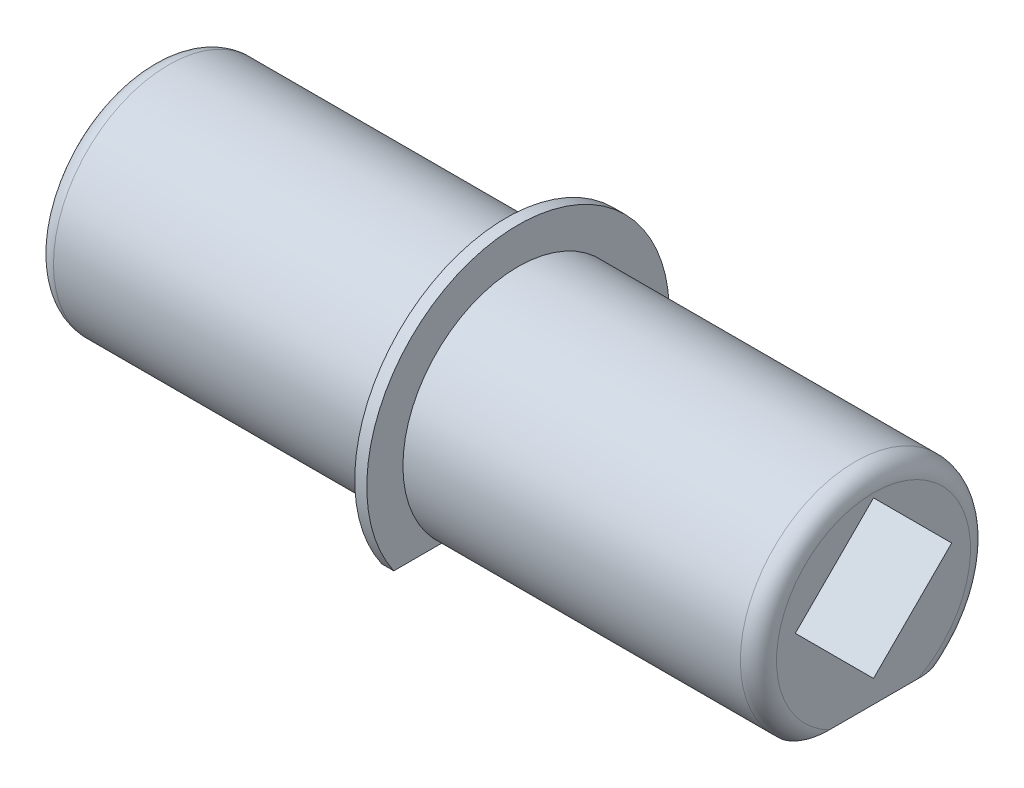
SolidWorks part; units mm, degrees
ref_plane "Plan de face" through (0, 0, 0) normal (0, 0, 1) x (1, 0, 0)
ref_plane "Plan de dessus" through (0, 0, 0) normal (0, 1, 0) x (1, 0, 0)
ref_plane "Plan de droite" through (0, 0, 0) normal (1, 0, 0) x (0, 0, -1)
sketch "Esquisse1" plane through (0, 0, 0) normal (1, 0, 0) x (0, 0, -1)
  line L0 (-6.3185, -7.161) -> (6.3185, -7.161)
  arc A0 (-6.3185, -7.161) -> (6.3185, -7.161) centre (0, 0) cw
  point P6 (0, -7.161)
  dimension "D1" = 9.55
extrude "Boss.-Extru.1" add sketch "Esquisse1" along normal mid plane 60
sketch "Esquisse3" plane through (0, 0, 0) normal (1, 0, 0) x (0, 0, -1)
  line L0 (-10.3065, -7.161) -> (10.3065, -7.161)
  line L1 (-6.3185, -7.161) -> (6.3185, -7.161) construction
  arc A2 (8.3034, -9.4105) -> (-8.3034, -9.4105) centre (0, 0) ccw
  arc A3 (10.3065, -7.161) -> (-10.3065, -7.161) centre (0, 0) ccw
  dimension "D1" = 3
extrude "Boss.-Extru.2" add sketch "Esquisse3" along normal mid plane 1
sketch "Esquisse2" plane through (0, 0, 0) normal (1, 0, 0) x (0, 0, -1)
  line L0 (0, 9.55) -> (0, 7.683) construction
  line L7 (0, -5.2939) -> (0, -7.161) construction
  line L8 (-6.3185, -7.161) -> (6.3185, -7.161) construction
  line L9 (-6.4884, 1.1945) -> (0, -5.2939)
  line L16 (-6.4884, 1.1945) -> (0, 7.683)
  line L17 (0, -5.2939) -> (6.4884, 1.1945)
  line L18 (0, 7.683) -> (6.4884, 1.1945)
  line L19 (-6.4884, 1.1945) -> (6.4884, 1.1945) construction
  line L20 (0, -5.2939) -> (0, 7.683) construction
  arc A1 (6.3185, -7.161) -> (-6.3185, -7.161) centre (0, 0) ccw construction
extrude "Enlèv. mat.-Extru.1" cut sketch "Esquisse2" against normal mid plane 100
fillet "Congé1" radius 1.5 2 edges at (-30, 9.55, 0) (30, 9.55, 0)
